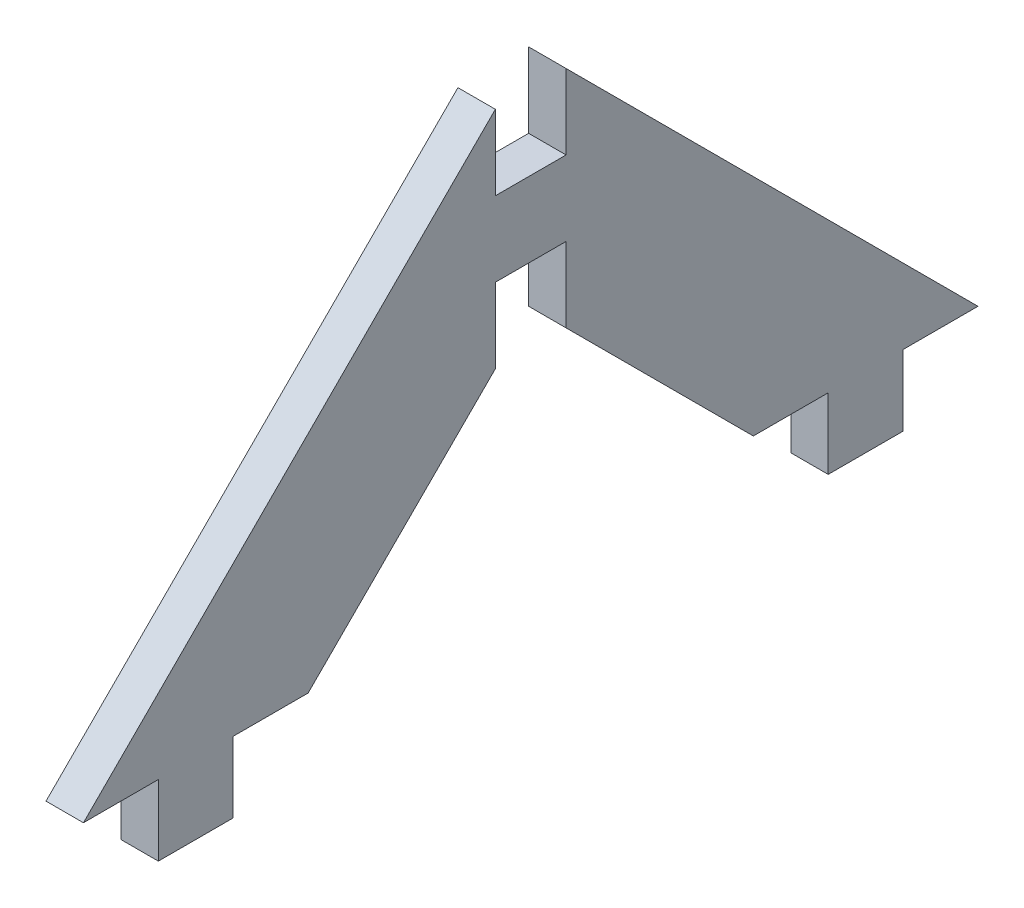
SolidWorks part; units mm, degrees
material "Acrylic (Medium-high impact)"
ref_plane "Front Plane" through (0, 0, 0) normal (0, 0, 1) x (1, 0, 0)
ref_plane "Top Plane" through (0, 0, 0) normal (0, 1, 0) x (1, 0, 0)
ref_plane "Right Plane" through (0, 0, 0) normal (1, 0, 0) x (0, 0, -1)
sketch "Sketch1" plane through (0, 0, 0) normal (1, 0, 0) x (0, 0, -1)
  line L0 (0, 0) -> (6.35, 0)
  line L1 (6.35, 0) -> (6.35, -5.9944)
  line L2 (6.35, -5.9944) -> (12.7, -5.9944)
  line L3 (12.7, -5.9944) -> (12.7, 0)
  line L4 (12.7, 0) -> (19.05, 0)
  line L5 (19.05, 0) -> (34.925, 15.875)
  line L6 (34.925, 15.875) -> (34.925, 22.225)
  line L7 (34.925, 22.225) -> (40.9194, 22.225)
  line L8 (40.9194, 22.225) -> (40.9194, 15.875)
  line L9 (40.9194, 15.875) -> (56.7944, 0)
  line L10 (56.7944, 0) -> (63.1444, 0)
  line L11 (63.1444, 0) -> (63.1444, -5.9944)
  line L12 (63.1444, -5.9944) -> (69.4944, -5.9944)
  line L13 (69.4944, -5.9944) -> (69.4944, 0)
  line L14 (69.4944, 0) -> (75.8444, 0)
  line L15 (75.8444, 0) -> (40.9194, 34.925)
  line L16 (40.9194, 34.925) -> (40.9194, 28.575)
  line L17 (40.9194, 28.575) -> (34.925, 28.575)
  line L18 (34.925, 28.575) -> (34.925, 34.925)
  line L19 (34.925, 34.925) -> (0, 0)
  dimension "D1" = 45
  dimension "D2" = 5.9944
  dimension "D3" = 5.9944
  dimension "D4" = 28.575
  dimension "D5" = 6.35
  dimension "D6" = 34.925
  dimension "D7" = 34.925
extrude "Boss-Extrude1" add sketch "Sketch1" along normal blind 3.175
